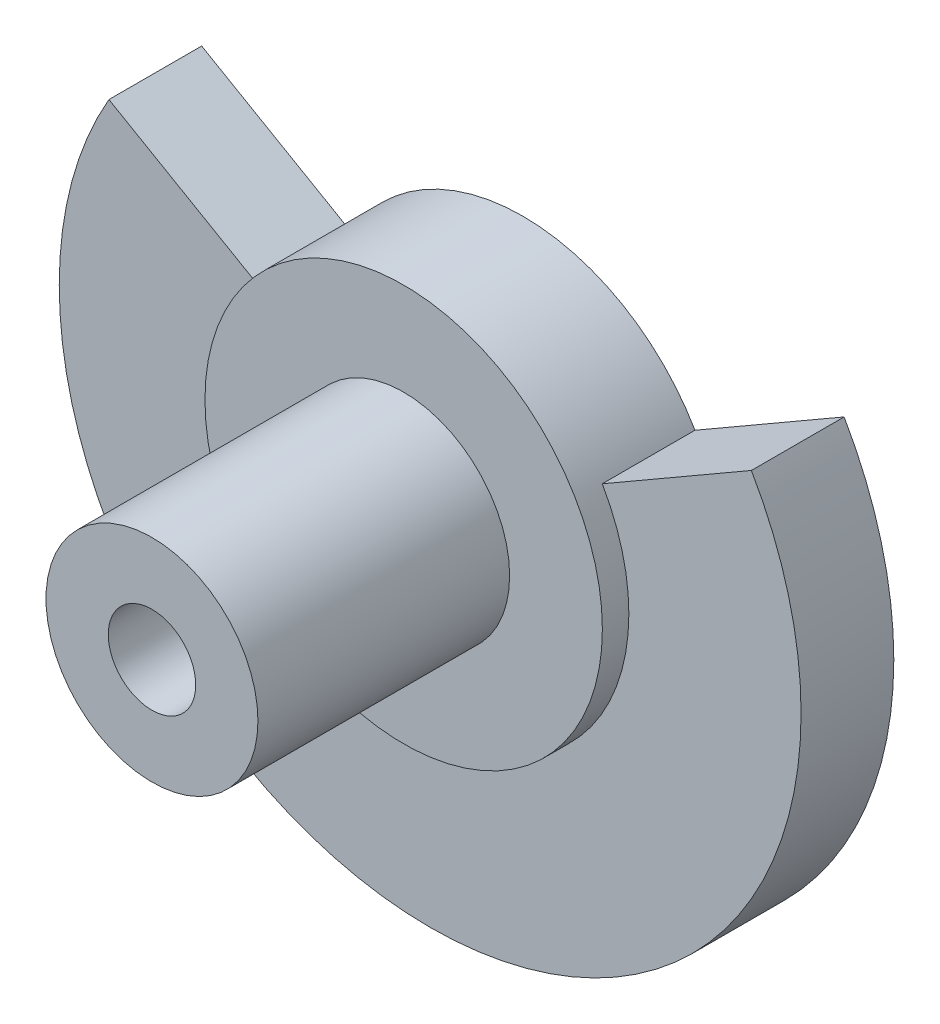
SolidWorks part; units mm, degrees
ref_plane "Front Plane" through (0, 0, 0) normal (0, 0, 1) x (1, 0, 0)
ref_plane "Top Plane" through (0, 0, 0) normal (0, 1, 0) x (1, 0, 0)
ref_plane "Right Plane" through (0, 0, 0) normal (1, 0, 0) x (0, 0, -1)
sketch "Sketch1" plane through (0, 0, 0) normal (0, 0, 1) x (1, 0, 0)
  circle A0 centre (0, 0) radius 14
  circle A1 centre (0, 0) radius 1.65
  dimension "D1" = 3.3
  dimension "D2" = 28
extrude "Boss-Extrude1" add sketch "Sketch1" along normal blind 14
sketch "Sketch2" plane through (0, 0, 14) normal (0, 0, 1) x (1, 0, 0)
  circle A0 centre (0, 0) radius 4
  circle A1 centre (0, 0) radius 14
  dimension "D1" = 8
extrude "Cut-Extrude1" cut sketch "Sketch2" against normal blind 9.5
sketch "Sketch3" plane through (0, 0, 4.5) normal (0, 0, 1) x (1, 0, 0)
  circle A0 centre (0, 0) radius 7.5
  circle A1 centre (0, 0) radius 14
  circle A2 centre (0, 0) radius 14 construction
  dimension "D1" = 15
extrude "Cut-Extrude2" cut sketch "Sketch3" against normal blind 1
sketch "Sketch4" plane through (0, 0, 3.5) normal (0, 0, 1) x (1, 0, 0)
  line L0 (6.4952, 3.75) -> (12.1244, 7)
  line L1 (-6.4952, 3.75) -> (-12.1244, 7)
  line L2 (0, -1000) -> (0, 49000) construction
  arc A0 (6.4952, 3.75) -> (-6.4952, 3.75) centre (0, 0) ccw
  arc A1 (12.1244, 7) -> (-12.1244, 7) centre (0, 0) ccw
  circle A2 centre (0, 0) radius 14 construction
  circle A3 centre (0, 0) radius 7.5 construction
  dimension "D1" = 120
extrude "Cut-Extrude3" cut sketch "Sketch4" against normal through all
